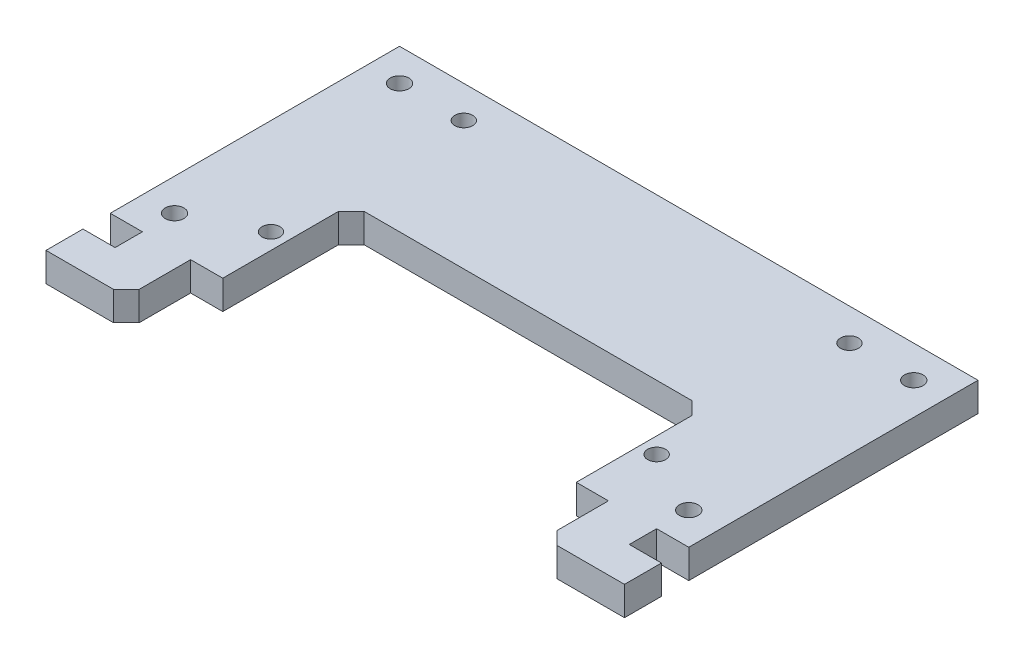
SolidWorks part; units mm, degrees
ref_plane "Front Plane" through (0, 0, 0) normal (0, 0, 1) x (1, 0, 0)
ref_plane "Top Plane" through (0, 0, 0) normal (0, 1, 0) x (1, 0, 0)
ref_plane "Right Plane" through (0, 0, 0) normal (1, 0, 0) x (0, 0, -1)
sketch "Sketch1" plane through (0, 0, 0) normal (0, 1, 0) x (1, 0, 0)
  line L1 (-45, 0) -> (45, 0)
  line L2 (-45, 0) -> (-45, -55)
  line L3 (-45, -55) -> (45, -55)
  line L4 (45, 0) -> (45, -55)
  line L5 (-40, -40) -> (40, -40) construction
  line L6 (-40, -40) -> (-40, -5) construction
  line L7 (-40, -5) -> (40, -5) construction
  line L8 (40, -40) -> (40, -5) construction
  circle A0 centre (-40, -40) radius 1.45
  circle A1 centre (-40, -5) radius 1.45
  circle A2 centre (40, -40) radius 1.45
  circle A3 centre (40, -5) radius 1.45
  dimension "D3" = 5
  dimension "D5" = 2.9
  dimension "D1" = 90
  dimension "D2" = 55
  dimension "D4" = 15
  dimension "D6" = 5
  dimension "D7" = 5
extrude "Boss-Extrude1" add sketch "Sketch1" along normal blind 4.5
sketch "Sketch2" plane through (0, 4.5, 0) normal (0, 1, 0) x (1, 0, 0)
  line L0 (-45, 0) -> (-45, -55) construction
  line L1 (-45, -45) -> (-40, -45)
  line L2 (-45, -45) -> (-45, -49.25)
  line L3 (-45, -49.25) -> (-40, -49.25)
  line L4 (-40, -45) -> (-40, -49.25)
  line L5 (45, -55) -> (45, 0) construction
  line L6 (45, -49.25) -> (40, -49.25)
  line L7 (45, -49.25) -> (45, -45)
  line L8 (45, -45) -> (40, -45)
  line L9 (40, -49.25) -> (40, -45)
  line L10 (45, 0) -> (-45, 0) construction
  dimension "D1" = 5
  dimension "D2" = 4.25
  dimension "D3" = 45
extrude "Cut-Extrude1" cut sketch "Sketch2" against normal through all
sketch "Sketch3" plane through (0, 4.5, 0) normal (0, 1, 0) x (1, 0, 0)
  circle A0 centre (-30, -35) radius 1.4
  circle A1 centre (-30, -5) radius 1.4
  point P4 (-40, -5)
  dimension "D1" = 2.8
  dimension "D2" = 30
  dimension "D3" = 30
extrude "Cut-Extrude2" cut sketch "Sketch3" against normal through all
mirror "Mirror1" about plane through (0, 0, 0) normal (1, 0, 0) of "Cut-Extrude2"
sketch "Sketch4" plane through (0, 4.5, 0) normal (0, 1, 0) x (1, 0, 0)
  line L0 (-45, -55) -> (45, -55) construction
  line L1 (-27.5, -55) -> (27.5, -55)
  line L2 (-27.5, -55) -> (-27.5, -25)
  line L3 (-27.5, -25) -> (27.5, -25)
  line L4 (27.5, -55) -> (27.5, -25)
  line L5 (0, -25) -> (0, 0) construction
  line L6 (45, 0) -> (-45, 0) construction
  dimension "D1" = 55
  dimension "D2" = 25
extrude "Cut-Extrude3" cut sketch "Sketch4" against normal through all
sketch "Sketch5" plane through (0, 4.5, 0) normal (0, 1, 0) x (1, 0, 0)
  line L0 (-45, -55) -> (-27.5, -55) construction
  line L1 (-32.5, -55) -> (32.5, -55)
  line L2 (-32.5, -55) -> (-32.5, -45)
  line L3 (-32.5, -45) -> (32.5, -45)
  line L4 (32.5, -55) -> (32.5, -45)
  line L5 (45, -45) -> (40, -45) construction
  line L6 (0, -45) -> (0, 0) construction
  dimension "D1" = 65
extrude "Cut-Extrude4" cut sketch "Sketch5" against normal through all
chamfer "Chamfer1" distance 2 angle 45 4 edges at (32.5, 2.25, 55) (27.5, 2.25, 25) (-27.5, 2.25, 25) (-32.5, 2.25, 55)
